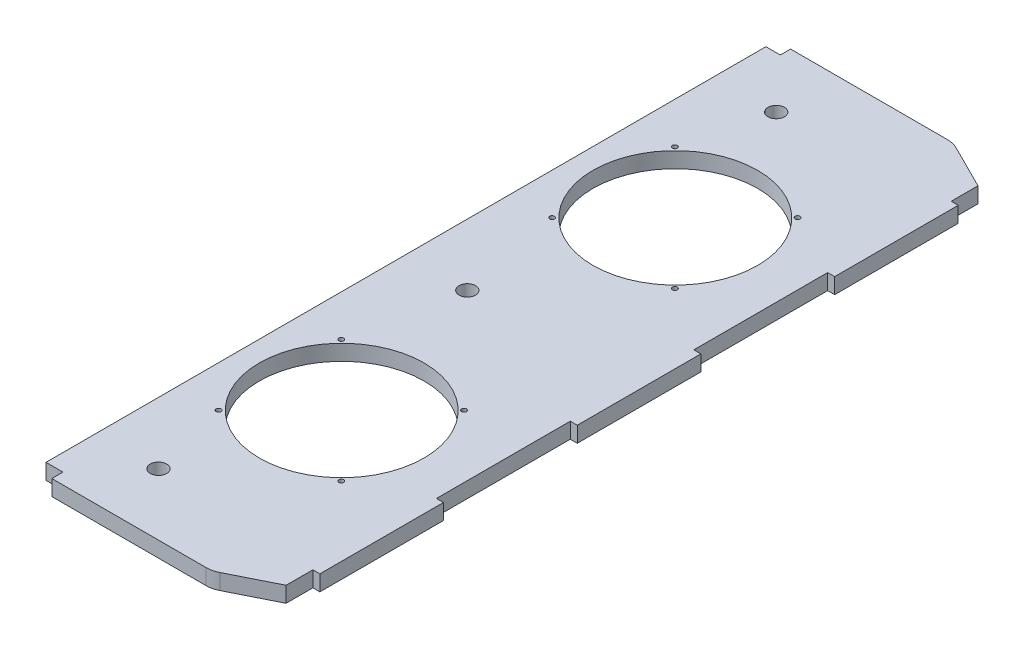
SolidWorks part; units mm, degrees
material "PE High Density"
ref_plane "Front Plane" through (0, 0, 0) normal (0, 0, 1) x (1, 0, 0)
ref_plane "Top Plane" through (0, 0, 0) normal (0, 1, 0) x (1, 0, 0)
ref_plane "Right Plane" through (0, 0, 0) normal (1, 0, 0) x (0, 0, -1)
sketch "Sketch1" plane through (0, 0, 0) normal (0, 1, 0) x (1, 0, 0)
  line L0 (0, 0) -> (0, 457.2)
  line L1 (0, 457.2) -> (139.7, 457.2)
  line L10 (139.7, 457.2) -> (139.7, 0)
  line L11 (139.7, 0) -> (0, 0)
  line L12 (0, 228.6) -> (139.7, 228.6) construction
  circle A0 centre (63.5, 125.73) radius 50.8
  circle A1 centre (38.1, 38.1) radius 5.08
  circle A3 centre (38.1, 419.1) radius 5.08
  circle A4 centre (63.5, 331.47) radius 50.8
  circle A5 centre (38.1, 228.6) radius 5.08
  dimension "D11" = 10.16
  dimension "D17" = 10.16
  dimension "D3" = 101.6
  dimension "D4" = 10.16
  dimension "D7" = 82.55
  dimension "D2" = 63.5
  dimension "Length of Rib" = 457.2
  dimension "D5" = 38.1
  dimension "D6" = 190.5
  dimension "D12" = 38.1
  dimension "D13" = 38.1
  dimension "D18" = 38.1
  dimension "D19" = 38.1
  dimension "Width of Rib" = 139.7
extrude "Boss-Extrude1" add sketch "Sketch1" along normal blind 9.652
sketch "Sketch4" plane through (0, 9.652, 0) normal (0, 1, 0) x (1, 0, 0)
  line L0 (10.4524, -8.5852) -> (10.4524, -21.2852) construction
  line L1 (0, 0) -> (10.4524, 0)
  line L2 (0, 0) -> (0, 6.858)
  line L3 (0, 6.858) -> (10.4524, 6.858)
  line L4 (10.4524, 0) -> (10.4524, 6.858)
  line L6 (0, 457.2) -> (8.8649, 457.2)
  line L7 (0, 457.2) -> (0, 450.85)
  line L8 (0, 450.85) -> (8.8649, 450.85)
  line L9 (8.8649, 457.2) -> (8.8649, 450.85)
  dimension "D1" = 6.858
extrude "Cut-Extrude1" cut sketch "Sketch4" against normal through all
chamfer "Chamfer1" distance 15.24 distance2 30.48 1 edges at (139.7, 4.826, -457.2)
chamfer "Chamfer2" distance 30.48 distance2 15.24 1 edges at (139.7, 4.826, 0)
fillet "Fillet2" radius 15.24 2 edges at (109.22, 4.826, -457.2) (109.22, 4.826, 0)
sketch "Sketch5" plane through (139.7, 0, 0) normal (1, 0, 0) x (0, 0, -1)
  line L0 (15.24, 9.652) -> (441.96, 9.652) construction
  line L1 (31.75, 9.652) -> (107.95, 9.652)
  line L2 (31.75, 9.652) -> (31.75, 0)
  line L3 (31.75, 0) -> (107.95, 0)
  line L4 (107.95, 9.652) -> (107.95, 0)
  line L5 (15.24, 0) -> (441.96, 0) construction
  line L6 (0, 0) -> (0, 9.652) construction
  line L7 (190.5, 9.652) -> (190.5, 0)
  line L8 (190.5, 9.652) -> (266.7, 9.652)
  line L9 (190.5, 0) -> (266.7, 0)
  line L10 (266.7, 9.652) -> (266.7, 0)
  line L11 (349.25, 9.652) -> (349.25, 0)
  line L12 (349.25, 9.652) -> (425.45, 9.652)
  line L13 (349.25, 0) -> (425.45, 0)
  line L14 (425.45, 9.652) -> (425.45, 0)
  dimension "D1" = 31.75
  dimension "D2" = 76.2
  dimension "D3" = 3
extrude "Boss-Extrude2" add sketch "Sketch5" along normal blind 4.318
sketch "Sketch7" plane through (0, 9.652, 0) normal (0, 1, 0) x (1, 0, 0)
  line L0 (10.4524, 0) -> (105.6223, 0) construction
  line L1 (139.7, 107.95) -> (139.7, 190.5) construction
  line L2 (101.092, 87.884) -> (101.092, 163.576) construction
  line L4 (101.092, 87.884) -> (25.4, 87.884) construction
  line L5 (25.4, 87.884) -> (25.4, 163.576) construction
  line L6 (25.4, 163.576) -> (101.092, 163.576) construction
  point P0 (101.092, 87.884)
  point P2 (25.4, 87.884)
  point P4 (25.4, 163.576)
  point P6 (101.092, 163.576)
  dimension "D1" = 87.884
  dimension "D2" = 38.608
  dimension "D3" = 75.692
  dimension "D4" = 75.692
  dimension "D5" = 75.692
  dimension "D6" = 75.692
hole_wizard "Ø3.0 (3) Diameter Hole1" positions "Sketch7" profile "Sketch8" hole size "Ø3.0" standard "ANSI Metric" end condition up to next
sketch "Sketch8" plane through (101.092, 9.652, -87.884) normal (1, 0, 0) x (0, 0, 1)
  line L0 (0, 0) -> (0, 9.652)
  line L1 (0, 9.652) -> (1.5, 9.652)
  line L2 (1.5, 9.652) -> (1.5, 0)
  line L5 (1.5, 0) -> (0, 0)
  line L11 (0, -6.35) -> (0, 107.95) construction
  dimension "Thru Hole Dia." = 3
  dimension "Thru Hole Depth" = 9.652
sketch "Sketch9" plane through (0, 9.652, 0) normal (0, 1, 0) x (1, 0, 0)
  line L0 (144.018, 228.6) -> (-0.0043, 228.6) construction
  line L1 (144.018, 266.7) -> (144.018, 190.5) construction
ref_plane "Plane1" through (0, 0, -228.6) normal (0, 0, 1) x (1, 0, 0)
mirror "Mirror1" about plane through (0, 0, -228.6) normal (0, 0, 1) of "Ø3.0 (3) Diameter Hole1"
